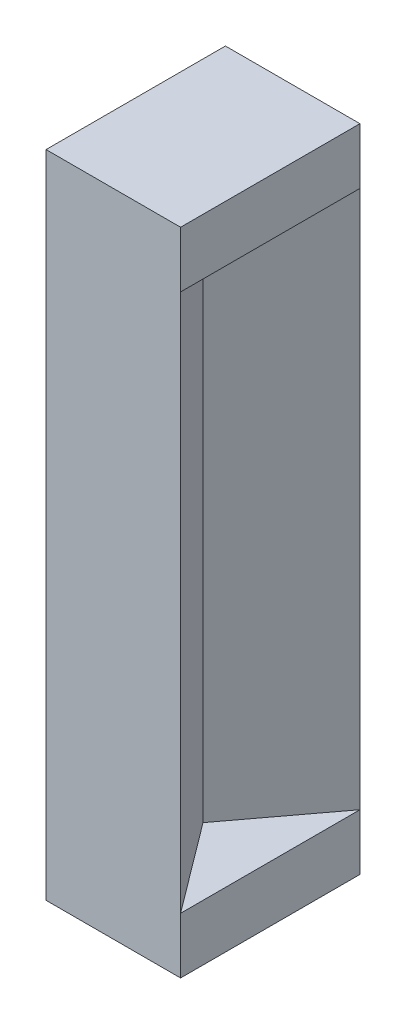
SolidWorks part; units mm, degrees
ref_plane "Front Plane" through (0, 0, 0) normal (0, 0, 1) x (1, 0, 0)
ref_plane "Top Plane" through (0, 0, 0) normal (0, 1, 0) x (1, 0, 0)
ref_plane "Right Plane" through (0, 0, 0) normal (1, 0, 0) x (0, 0, -1)
sketch "Sketch3" plane through (0, -266.5409, 0) normal (0, -1, 0) x (-1, 0, 0)
  line L1 (-120, 0) -> (-180, 0)
  line L2 (-180, 0) -> (-180, 80)
  line L3 (-180, 80) -> (-120, 80)
  line L5 (-120, 80) -> (-120, 0)
  dimension "D1" = 60
  dimension "D2" = 80
extrude "Boss-Extrude1" add sketch "Sketch3" along normal blind 25 contours L3 L5 L1 L2
sketch "Sketch4" plane through (0, -26.5409, 0) normal (0, 1, 0) x (1, 0, 0)
  line L1 (120, 80) -> (180, 80)
  line L2 (180, 80) -> (180, 0)
  line L3 (180, 0) -> (120, 0)
  line L4 (120, 0) -> (120, 80)
extrude "Boss-Extrude2" add sketch "Sketch4" along normal blind 25 separate body
sketch "Sketch5" plane through (0, -266.5409, 0) normal (0, 1, 0) x (1, 0, 0)
  line L0 (120, 80) -> (180, 0)
  line L1 (180, 0) -> (120, 0)
  line L2 (120, 0) -> (120, 80)
extrude "Boss-Extrude3" add sketch "Sketch5" along normal up to surface (240 mm away) up to face at (150, -26.5409, -40)
sketch "Sketch6" plane through (0, -266.5409, 0) normal (0, 1, 0) x (1, 0, 0)
  line L0 (120, 80) -> (180, 80)
  line L1 (180, 80) -> (120, 0)
  line L2 (120, 0) -> (120, 80)
extrude "Boss-Extrude4" add sketch "Sketch6" along normal up to surface (240 mm away) up to face at (160, -26.5409, -53.3333)
